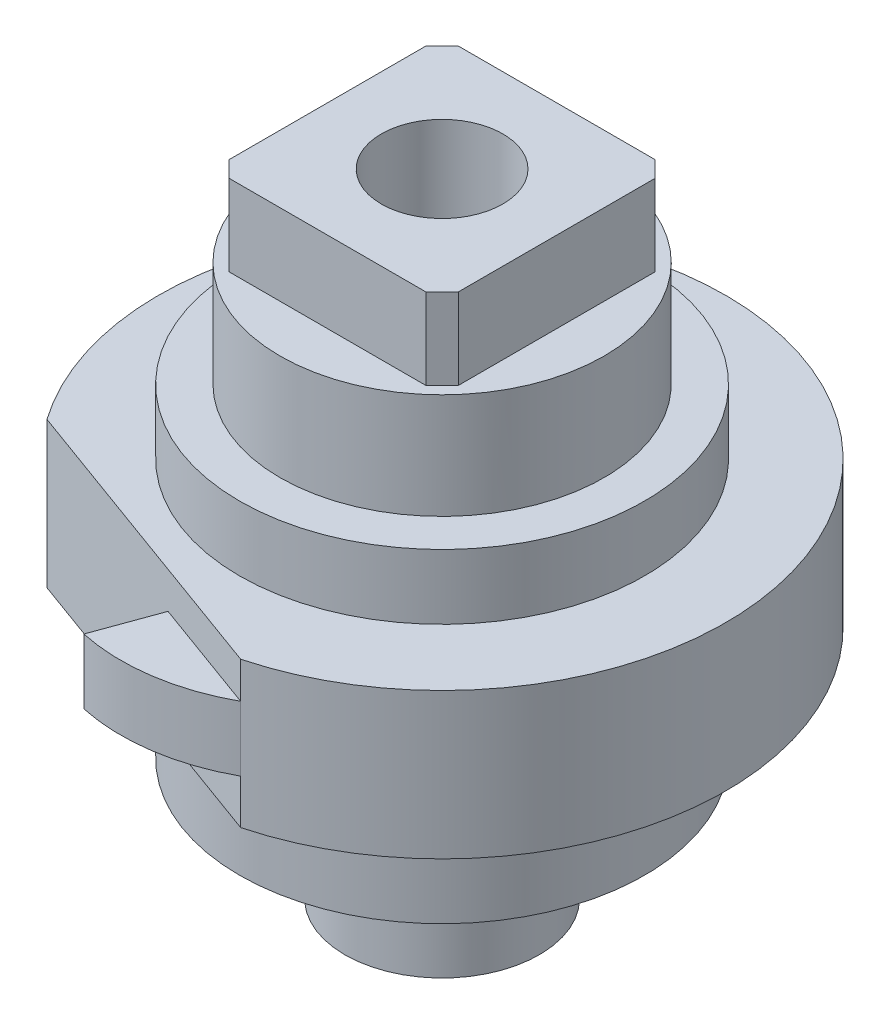
SolidWorks part; units mm, degrees
ref_plane "Alzado" through (0, 0, 0) normal (0, 0, 1) x (1, 0, 0)
ref_plane "Planta" through (0, 0, 0) normal (0, 1, 0) x (1, 0, 0)
ref_plane "Vista lateral" through (0, 0, 0) normal (1, 0, 0) x (0, 0, -1)
ref_plane "Plane1" through (0, -1.025, 0) normal (0, -1, 0) x (1, 0, 0)
sketch "Sketch1" plane through (0, -1.025, 0) normal (0, -1, 0) x (1, 0, 0)
  line L0 (0.4485, 1.6916) -> (-1.4309, 1.0075)
  arc A0 (-1.4309, 1.0075) -> (0.4485, 1.6916) centre (0, 0) ccw
  dimension "D1" = 1.75
  dimension "D2" = 0.4485
  dimension "D3" = 1.8794
extrude "Boss-Extrude1" add sketch "Sketch1" against normal blind 0.625
sketch "Sketch2" plane through (0, -0.4, 0) normal (0, 1, 0) x (-1, 0, 0)
  circle A0 centre (0, 0) radius 1.25
  dimension "D1" = 2.5
  dimension "D2" = 1.4309
  dimension "D3" = 1.6916
extrude "Boss-Extrude2" add sketch "Sketch2" along normal blind 0.4
sketch "Sketch3" plane through (0, 0, 0) normal (0, 1, 0) x (-1, 0, 0)
  circle A0 centre (0, 0) radius 1
  dimension "D1" = 2
extrude "Boss-Extrude3" add sketch "Sketch3" along normal blind 0.65
sketch "Sketch4" plane through (0, 0.65, 0) normal (0, 1, 0) x (-1, 0, 0)
  line L0 (0.7071, 0.7071) -> (0.7071, -0.7071)
  line L1 (0.7071, -0.7071) -> (-0.7071, -0.7071)
  line L2 (-0.7071, -0.7071) -> (-0.7071, 0.7071)
  line L3 (-0.7071, 0.7071) -> (0.7071, 0.7071)
  circle A0 centre (0, 0) radius 1 construction
  dimension "D1" = 0.7071
  dimension "D2" = 0.7071
  dimension "D3" = 0.7071
  dimension "D4" = 0.7071
extrude "Boss-Extrude4" add sketch "Sketch4" along normal blind 0.5
sketch "Sketch5" plane through (0, -1.025, 0) normal (0, -1, 0) x (1, 0, 0)
  line L0 (-0.3949, 1.816) -> (-0.2563, 1.435)
  line L1 (-0.2563, 1.435) -> (0.4485, 1.6916)
  arc A0 (0.4485, 1.6916) -> (-0.3949, 1.816) centre (-0.1401, 0.6226) ccw
  dimension "D1" = 1.2202
  dimension "D2" = 0.1386
  dimension "D3" = 0.2548
  dimension "D4" = 0.8434
  dimension "D5" = 0.8124
extrude "Boss-Extrude5" add sketch "Sketch5" against normal blind 0.4
sketch "Sketch6" plane through (0, -1.025, 0) normal (0, -1, 0) x (1, 0, 0)
  line L0 (-1.4309, 1.0075) -> (0.4485, 1.6916)
  arc A0 (0.4485, 1.6916) -> (-1.4309, 1.0075) centre (0, 0) cw
  dimension "D1" = 1.75
  dimension "D2" = 0.4485
  dimension "D3" = 1.8794
extrude "Boss-Extrude6" add sketch "Sketch6" along normal blind 0.275
ref_plane "Plane2" through (0, 0, 0) normal (0, 0, -1) x (-1, 0, 0)
sketch "Sketch7" plane through (0, 0, 0) normal (0, 0, -1) x (-1, 0, 0)
  line L0 (-0.6, -2.75) -> (0, -2.75)
  line L1 (0, -2.75) -> (0, -1.3)
  line L2 (0, -1.3) -> (-1.25, -1.3)
  line L3 (-1.25, -1.3) -> (-1.25, -2)
  line L4 (-1.25, -2) -> (-0.6, -2)
  line L5 (-0.6, -2) -> (-0.6, -2.75)
  line L6 (0, -2.75) -> (0, -1.3) construction
  dimension "D1" = 0.65
  dimension "D2" = 1.25
  dimension "D3" = 0.75
  dimension "D4" = 1.45
revolve "Revolve1" add sketch "Sketch7" angle 360 about L6
hole_wizard "Hole1" positions "Sketch9" profile "Sketch8" legacy
sketch "Sketch9" plane through (0, 1.15, 0) normal (0, 1, 0) x (1, 0, 0)
  point P0 (0, 0)
sketch "Sketch8" plane through (0, 1.15, 0) normal (1, 0, 0) x (0, 0, 1)
  line L0 (0, 0) -> (0, 2)
  line L1 (0, 2) -> (0.375, 2)
  line L2 (0.375, 2) -> (0.375, 0)
  line L3 (0.375, 0) -> (0, 0)
  line L4 (0, 110) -> (0, -10) construction
  dimension "Diameter" = 0.75
  dimension "Depth" = 2
chamfer "Chamfer1" distance 0.1 angle 45 4 edges at (0.7071, 0.9, -0.7071) (-0.7071, 0.9, -0.7071) (-0.7071, 0.9, 0.7071) (0.7071, 0.9, 0.7071)
